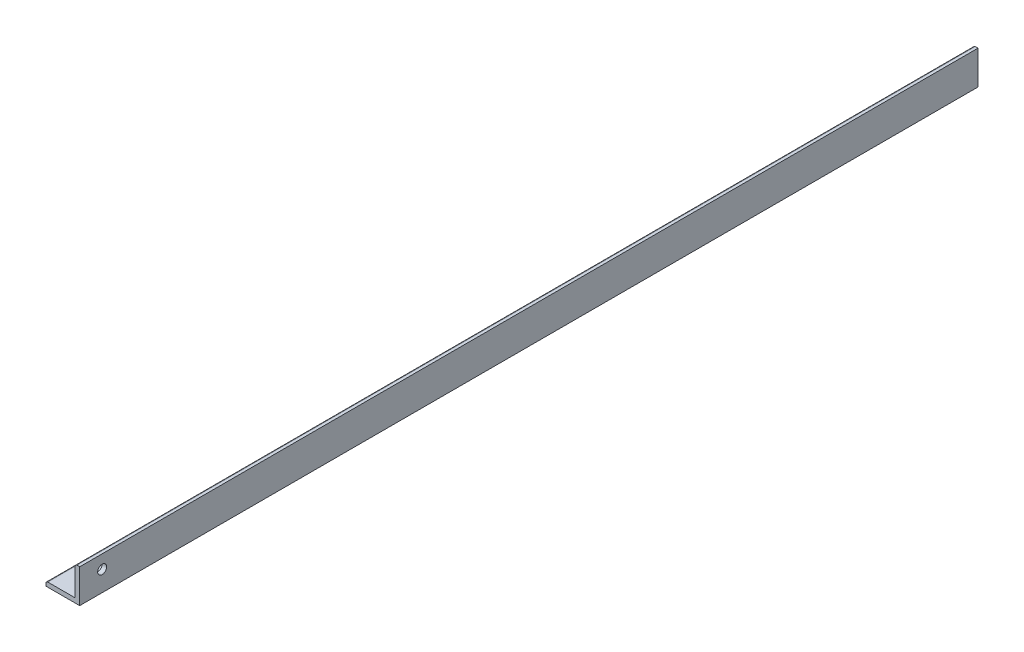
SolidWorks part; units mm, degrees
ref_plane "前视基准面" through (0, 0, 0) normal (0, 0, 1) x (1, 0, 0)
ref_plane "上视基准面" through (0, 0, 0) normal (0, 1, 0) x (1, 0, 0)
ref_plane "右视基准面" through (0, 0, 0) normal (1, 0, 0) x (0, 0, -1)
sketch "草图1" plane through (0, 0, 0) normal (0, 0, 1) x (1, 0, 0)
  line L0 (0, 0) -> (0, 15)
  line L1 (0, 15) -> (-2, 15)
  line L2 (-2, 15) -> (-2, 2)
  line L3 (0, 0) -> (-15, 0)
  line L4 (-15, 0) -> (-15, 2)
  line L5 (-15, 2) -> (-2, 2)
  dimension "D1" = 15
  dimension "D2" = 15
  dimension "D3" = 2
  dimension "D4" = 2
extrude "凸台-拉伸1" add sketch "草图1" along normal blind 400
fillet "圆角1" radius 0.8 2 edges at (-15, 2, 200) (-2, 15, 200)
sketch "草图2" plane through (0, 2, 0) normal (0, 1, 0) x (1, 0, 0)
  line L2 (-2, -400) -> (-2, 0) construction
  line L4 (-2, 0) -> (-14.2, 0) construction
  circle A1 centre (-8, -222) radius 2
  dimension "D1" = 4
  dimension "D2" = 222
  dimension "D6" = 6
extrude "切除-拉伸1" cut sketch "草图2" against normal blind 2
sketch "草图3" plane through (-2, 0, 0) normal (-1, 0, 0) x (0, 0, 1)
  line L0 (400, 14.2) -> (400, 2) construction
  line L2 (400, 2) -> (0, 2) construction
  circle A0 centre (390, 9) radius 2
  dimension "D1" = 4
  dimension "D2" = 10
  dimension "D3" = 7
extrude "切除-拉伸2" cut sketch "草图3" against normal blind 400
